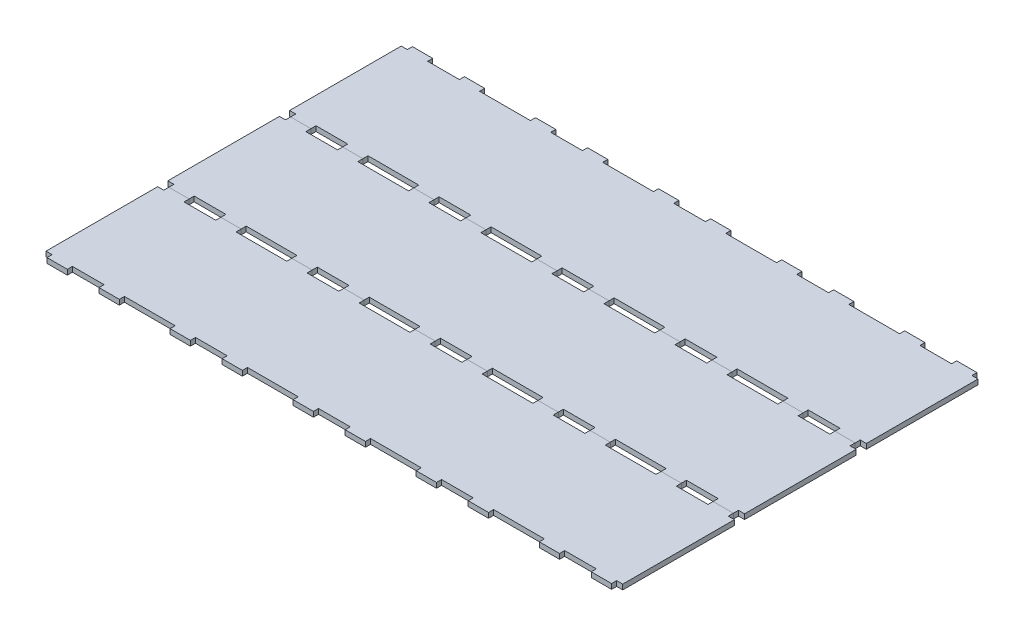
SolidWorks part; units mm, degrees
material "Cedar"
ref_plane "Front Plane" through (0, 0, 0) normal (0, 0, 1) x (1, 0, 0)
ref_plane "Top Plane" through (0, 0, 0) normal (0, 1, 0) x (1, 0, 0)
ref_plane "Right Plane" through (0, 0, 0) normal (1, 0, 0) x (0, 0, -1)
sketch "Sketch1" plane through (0, 0, 0) normal (0, 1, 0) x (1, 0, 0)
  line L1 (-360.8183, 76.2) -> (360.8183, 76.2)
  line L2 (-360.8183, 76.2) -> (-360.8183, -76.2)
  line L3 (-360.8183, -76.2) -> (360.8183, -76.2)
  line L4 (360.8183, 76.2) -> (360.8183, -76.2)
  line L5 (-360.8183, 76.2) -> (360.8183, -76.2) construction
  line L6 (-360.8183, -76.2) -> (360.8183, 76.2) construction
  point P0 (0, 0)
  dimension "D1" = 721.6366
  dimension "D2" = 152.4
extrude "Boss-Extrude1" add sketch "Sketch1" along normal blind 6.35
sketch "Sketch2" plane through (0, 6.35, 0) normal (0, 1, 0) x (1, 0, 0)
  line L0 (0, -76.2) -> (0, -69.85) construction
  line L1 (-32.5397, -69.85) -> (32.5397, -69.85) construction
  line L2 (-45.2397, -69.85) -> (-19.8397, -69.85) construction
  line L3 (-45.2397, -69.85) -> (-45.2397, -76.2) construction
  line L4 (-45.2397, -76.2) -> (-19.8397, -76.2) construction
  line L5 (-19.8397, -69.85) -> (-19.8397, -76.2)
  line L6 (-45.2397, -69.85) -> (-19.8397, -76.2) construction
  line L7 (-45.2397, -76.2) -> (-19.8397, -69.85) construction
  line L8 (-360.8183, -76.2) -> (360.8183, -76.2) construction
  line L9 (-19.8397, -69.85) -> (19.8397, -69.85)
  line L10 (19.8397, -69.85) -> (45.2397, -69.85) construction
  line L11 (19.8397, -69.85) -> (19.8397, -76.2)
  line L12 (19.8397, -76.2) -> (45.2397, -76.2) construction
  line L13 (45.2397, -69.85) -> (45.2397, -76.2) construction
  line L14 (19.8397, -69.85) -> (45.2397, -76.2) construction
  line L15 (19.8397, -76.2) -> (45.2397, -69.85) construction
  line L16 (19.8397, -76.2) -> (-19.8397, -76.2)
  line L17 (-45.2397, -76.2) -> (-45.2397, -69.85)
  line L18 (-45.2397, -69.85) -> (-76.9897, -69.85)
  line L19 (-76.9897, -69.85) -> (-76.9897, -76.2)
  line L20 (-76.9897, -76.2) -> (-45.2397, -76.2)
  line L21 (45.2397, -69.85) -> (76.9897, -69.85)
  line L22 (76.9897, -69.85) -> (76.9897, -76.2)
  line L23 (76.9897, -76.2) -> (45.2397, -76.2)
  line L24 (45.2397, -76.2) -> (45.2397, -69.85)
  point P5 (0, -69.85)
  point P6 (-32.5397, -73.025)
  point P11 (-32.5397, -69.85)
  point P17 (32.5397, -73.025)
  point P24 (32.5397, -69.85)
  dimension "D1" = 39.6793
  dimension "D2" = 25.4
  dimension "D3" = 6.35
  dimension "D4" = 76.9897
  dimension "D5" = 25.4
  dimension "D6" = 6.35
  dimension "D7" = 76.9897
extrude "Cut-Extrude1" cut sketch "Sketch2" against normal through all
pattern_linear "LPattern1" count 3 spacing 153.9793 along (1, 0, 0) count 3 spacing 153.9793 along (-1, 0, 0) of "Cut-Extrude1"
mirror "Mirror1" about plane through (0, 0, 0) normal (0, 0, 1) of "LPattern1", "Cut-Extrude1"
pattern_linear "LPattern2" count 3 spacing 152.4 along (0, 0, 1) of bodies 104
